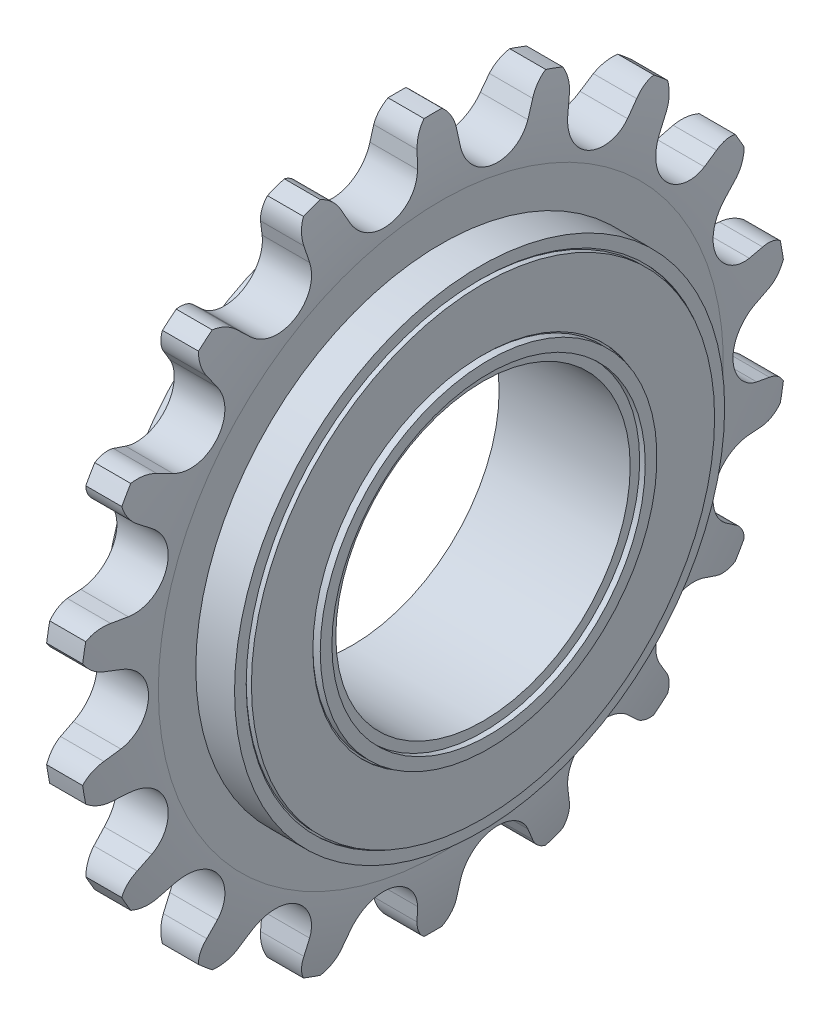
SolidWorks part; units mm, degrees
ref_plane "Front Plane" through (0, 0, 0) normal (0, 0, 1) x (1, 0, 0)
ref_plane "Top Plane" through (0, 0, 0) normal (0, 1, 0) x (1, 0, 0)
ref_plane "Right Plane" through (0, 0, 0) normal (1, 0, 0) x (0, 0, -1)
sketch "Layout with Teeth" plane through (0, 0, 0) normal (1, 0, 0) x (0, 0, -1)
  line L0 (0, 0) -> (0, 66.6612) construction
  line L5 (-11.5756, 65.6485) -> (0, 66.6612) construction
  line L6 (0, 0) -> (-11.5756, 65.6485) construction
  line L7 (0, 0) -> (11.5756, 65.6485) construction
  line L8 (2.3757, 35.5598) -> (-2.3757, 35.5598)
  line L9 (-2.3757, 35.5598) -> (-2.1798, 37.2772)
  line L10 (2.3757, 35.5598) -> (2.1803, 37.2772)
  line L11 (0, 66.6612) -> (11.5756, 65.6485) construction
  circle A0 centre (0, 0) radius 17.4625
  circle A1 centre (0, 0) radius 36.5682
  circle A2 centre (0, 0) radius 39.4882
  circle A7 centre (0, 0) radius 32.5682 construction
  circle A8 centre (0, 0) radius 18.52
  circle A9 centre (0, 0) radius 19.82
  circle A10 centre (0, 0) radius 20.02
  circle A11 centre (0, 0) radius 25.815
  circle A12 centre (0, 0) radius 26.015
  circle A13 centre (0, 0) radius 27.315
  arc A14 (-0.9993, 39.4755) -> (-2.1798, 37.2772) centre (1.1685, 36.8953) ccw
  arc A15 (1.0007, 39.4755) -> (2.1803, 37.2772) centre (-1.1681, 36.8962) cw
  circle A16 centre (6.35, 36.0126) radius 4
  circle A17 centre (-6.35, 36.0126) radius 4
  dimension "D2" = 8
  dimension "D3" = 3.37
  dimension "D4" = 2.92
  dimension "D5" = 78.9764
  dimension "D6" = 73.1364
  dimension "D7" = 34.925
  dimension "D9" = 12.7
  dimension "D11" = 37.04
  dimension "D12" = 39.64
  dimension "D13" = 40.04
  dimension "D14" = 51.63
  dimension "D15" = 52.03
  dimension "D16" = 54.63
  dimension "D18" = 3.37
  dimension "D20" = 8
  dimension "D8" = 13
  dimension "D10" = 20
  dimension "D17" = 1.7285
  dimension "D19" = 1.7285
  dimension "D21" = 2
  dimension "D22" = 4.7514
  dimension "D23" = 11.5756
sketch "Side Layout" plane through (0, 0, 0) normal (0, 0, 1) x (1, 0, 0)
  line L0 (2.8829, 31.4882) -> (2.8829, 27.3125)
  line L1 (2.8829, 27.3125) -> (7.2, 27.3125)
  line L2 (0, -39.4882) -> (0, 39.4882) construction
  line L3 (0, 0) -> (0, 66.6612) construction
  line L4 (2.0077, 39.4882) -> (-2.0077, 39.4882)
  line L5 (-2.8829, 31.4882) -> (-2.8829, 27.3125)
  line L6 (-2.8829, 27.3125) -> (-7.2, 27.3125)
  line L7 (-7.2, 27.3125) -> (-7.2, 25.8125)
  line L8 (-7.58, 25.8125) -> (-4, 25.8125)
  line L9 (-4, 25.8125) -> (-4, 18.9625)
  line L10 (-7.58, 16.4042) -> (7.2, 16.4042)
  line L11 (0, 0) -> (0, 47.8969) construction
  line L12 (7.2, 27.3125) -> (7.2, 25.8125)
  line L13 (7.58, 25.8125) -> (4, 25.8125)
  line L14 (-2.8829, 31.4882) -> (0, 31.4882) construction
  line L18 (-4, 18.9625) -> (-8.2, 18.9625)
  line L19 (-7.58, 17.4625) -> (-8.2, 17.4625)
  line L20 (-8.2, 18.9625) -> (-8.2, 17.4625)
  line L21 (-7.58, 18.9625) -> (-7.58, 25.8125)
  line L22 (4, 18.9625) -> (7.58, 18.9625)
  line L23 (7.2, 18.9625) -> (7.2, 16.4042)
  line L24 (7.58, 18.9625) -> (7.58, 25.8125)
  line L25 (4, 25.8125) -> (4, 18.9625)
  line L26 (-7.58, 17.4625) -> (-7.58, 16.4042)
  arc A0 (-2.0077, 39.4882) -> (-2.8829, 31.4882) centre (34.1171, 31.4882) ccw
  arc A1 (2.0077, 39.4882) -> (2.8829, 31.4882) centre (-34.1171, 31.4882) cw
  point P0 (0, 39.4882)
  point P30 (0, 39.4882)
  point P38 (0, 17.4625)
  dimension "D14" = 37
  dimension "D1" = 9.4083
  dimension "D2" = 4.1757
  dimension "D4" = 1.5
  dimension "D7" = 10.9083
  dimension "D9" = 8
  dimension "D5" = 4.0154
  dimension "D6" = 5.7658
  dimension "D3" = 14.4
  dimension "D10" = 1
  dimension "D11" = 15.16
  dimension "D12" = 1.5
  dimension "D8" = 1.0583
  dimension "D13" = 8
sketch "Threaded Hole Layout" plane through (0, 0, 0) normal (0, 0, 1) x (1, 0, 0)
  line L1 (-7.58, 17.3625) -> (-7.63, 17.2759) construction
  line L2 (-8.191, 16.3042) -> (-8.141, 16.3042) construction
  line L3 (-6.969, 16.3042) -> (-7.019, 16.3908) construction
  line L4 (-7.58, 17.4625) -> (-7.58, 16.4042) construction
  line L5 (-7.58, 16.4042) -> (7.2, 16.4042) construction
  line L6 (-7.63, 17.2759) -> (-7.53, 17.2759)
  line L7 (-7.019, 16.3908) -> (-7.019, 16.3042)
  line L8 (-8.141, 16.3908) -> (-8.141, 16.3042)
  line L9 (-7.63, 17.2759) -> (-8.141, 16.3908)
  line L10 (-7.53, 17.2759) -> (-7.58, 17.3625) construction
  line L13 (-8.141, 16.3908) -> (-8.191, 16.3042) construction
  line L14 (-8.141, 16.3042) -> (-7.019, 16.3042)
  line L15 (-7.019, 16.3042) -> (-6.969, 16.3042) construction
  line L16 (-7.019, 16.3908) -> (-7.53, 17.2759)
  circle A0 centre (-7.58, 16.6569) radius 0.3528 construction
  dimension "D1" = 1.0583
  dimension "D2" = 0.1
  dimension "D3" = 0.1
  dimension "D4" = 0.05
sketch "Sketch8" plane through (0, 0, 0) normal (1, 0, 0) x (0, 0, -1)
  line L0 (0, 0) -> (-11.5756, 65.6485) construction
  circle A0 centre (0, 0) radius 36.5682 construction
  point P0 (-6.35, 36.0126)
  point P1 (-28.0129, 23.5056)
  point P2 (-18.2841, 31.669)
  point P4 (6.35, 36.0126)
  point P5 (18.2841, 31.669)
  point P6 (28.0129, 23.5056)
  point P7 (34.3629, 12.5071)
  point P8 (36.5682, 0)
  point P9 (34.3629, -12.5071)
  point P10 (28.0129, -23.5056)
  point P11 (18.2841, -31.669)
  point P12 (6.35, -36.0126)
  point P13 (-6.35, -36.0126)
  point P14 (-18.2841, -31.669)
  point P15 (-28.0129, -23.5056)
  point P16 (-34.3629, -12.5071)
  point P17 (-36.5682, 0)
  point P18 (-34.3629, 12.5071)
  point P19 (0, 0)
  dimension "D1" = 18
ref_axis "Axis1" through (0, 0, 0) along (1, 0, 0)
sketch "Sketch4" plane through (0, 0, 0) normal (1, 0, 0) x (0, 0, -1)
  line L0 (-2.3757, 35.5598) -> (-2.1798, 37.2772) construction
  line L1 (2.3757, 35.5598) -> (2.1803, 37.2772) construction
  line L2 (0, 0) -> (-11.5756, 65.6485) construction
  line L3 (0, 0) -> (11.5756, 65.6485) construction
  line L8 (-2.3758, 35.5593) -> (-2.1798, 37.2772)
  line L9 (2.3757, 35.5603) -> (2.1803, 37.2772)
  line L10 (0, 0) -> (-5.6554, 32.0734)
  line L11 (0, 0) -> (5.6554, 32.0734)
  arc A1 (-0.9993, 39.4755) -> (-2.1798, 37.2772) centre (1.1685, 36.8953) ccw construction
  arc A2 (2.1803, 37.2772) -> (1.0007, 39.4755) centre (-1.1681, 36.8962) ccw construction
  circle A3 centre (-6.35, 36.0126) radius 4 construction
  circle A4 centre (6.35, 36.0126) radius 4 construction
  arc A7 (-0.9993, 39.4755) -> (-2.1798, 37.2772) centre (1.1685, 36.8953) ccw
  arc A9 (2.1803, 37.2772) -> (1.0007, 39.4755) centre (-1.1681, 36.8962) ccw
  arc A10 (-5.6554, 32.0734) -> (-2.3758, 35.5593) centre (-6.35, 36.0126) ccw
  arc A11 (2.3757, 35.5603) -> (5.6554, 32.0734) centre (6.35, 36.0126) ccw
  arc A14 (1.0007, 39.4755) -> (-0.9993, 39.4755) centre (0, 0) ccw
extrude "Boss-Extrude1" add sketch "Sketch4" along normal mid plane 17
pattern_circular "CirPattern2" count 18 over 360 about axis through (0, 0, 0) along (1, 0, 0) of "Boss-Extrude1"
sketch "Sketch6" plane through (0, 0, 0) normal (0, 0, 1) x (1, 0, 0)
  line L0 (7.2, 27.3125) -> (7.2, 25.8125) construction
  line L1 (0, 39.4882) -> (0, 16.4042) construction
  line L2 (7.58, 18.9625) -> (7.58, 25.8125) construction
  line L3 (2.0077, 39.4882) -> (-2.0077, 39.4882) construction
  line L4 (-10, 39.4882) -> (-10, 0)
  line L5 (-2.0077, 39.4882) -> (-10, 39.4882)
  line L6 (10, 39.4882) -> (10, 0)
  line L7 (2.0077, 39.4882) -> (10, 39.4882)
  line L8 (7, 26.0125) -> (7.2, 26.0125)
  line L9 (-7, 26.0125) -> (-7, 25.8125)
  line L10 (-7.2, 26.0125) -> (-7, 26.0125)
  line L11 (7, 25.8125) -> (7, 26.0125)
  line L12 (7.38, 18.7625) -> (8.2, 18.7625)
  line L13 (7.38, 18.9625) -> (7.38, 18.7625)
  line L14 (2.8829, 31.4882) -> (2.8829, 27.3125)
  line L15 (2.8829, 27.3125) -> (7.2, 27.3125)
  line L16 (7.2, 27.3125) -> (7.2, 26.0125)
  line L17 (7.58, 25.8125) -> (7, 25.8125)
  line L18 (7.58, 18.9625) -> (7.58, 25.8125)
  line L19 (7.38, 18.9625) -> (7.58, 18.9625)
  line L20 (8.2, 18.7625) -> (8.2, 17.4625)
  line L21 (7.58, 17.4625) -> (8.2, 17.4625)
  line L22 (-7.58, 17.4625) -> (-8.2, 17.4625) construction
  line L23 (-7.2, 27.3125) -> (-7.2, 25.8125) construction
  line L24 (-7.58, 18.9625) -> (-7.58, 25.8125) construction
  line L25 (-7.58, 16.4042) -> (7.2, 16.4042) construction
  line L26 (-2.8829, 27.3125) -> (-7.2, 27.3125) construction
  line L27 (-7.58, 25.8125) -> (-4, 25.8125) construction
  line L28 (7.58, 25.8125) -> (4, 25.8125) construction
  line L29 (2.0077, 39.4882) -> (-2.0077, 39.4882) construction
  line L35 (7.58, 17.4625) -> (7.58, 16.4042)
  line L65 (7.58, 16.4042) -> (-7.2, 16.4042)
  line L68 (-7.2, 18.9625) -> (-7.2, 16.4042)
  line L69 (-7.2, 18.9625) -> (-7.58, 18.9625)
  line L70 (-7.58, 18.9625) -> (-7.58, 25.8125)
  line L71 (-7.58, 25.8125) -> (-7, 25.8125)
  line L72 (-7.2, 27.3125) -> (-7.2, 26.0125)
  line L73 (-2.8829, 27.3125) -> (-7.2, 27.3125)
  line L74 (-2.8829, 31.4882) -> (-2.8829, 27.3125)
  line L75 (10, 0) -> (-10, 0)
  arc A0 (2.0077, 39.4882) -> (2.8829, 31.4882) centre (-34.1171, 31.4882) cw
  arc A1 (-2.8829, 31.4882) -> (-2.0077, 39.4882) centre (34.1171, 31.4882) cw
  arc A2 (2.8829, 31.4882) -> (2.0077, 39.4882) centre (-34.1171, 31.4882) ccw construction
  arc A3 (-2.0077, 39.4882) -> (-2.8829, 31.4882) centre (34.1171, 31.4882) ccw construction
  dimension "D1" = 0.2
  dimension "D2" = 20
  dimension "D3" = 0.82
  dimension "D4" = 0.2
  dimension "D5" = 0.2
  dimension "D6" = 1.3
  dimension "D7" = 0.38
  dimension "D8" = 2.5583
revolve "Cut-Revolve1" cut sketch "Sketch6" angle 360 about axis through (0, 0, 0) along (1, 0, 0)
sketch "Sketch7" plane through (0, 0, 0) normal (0, 0, 1) x (1, 0, 0)
  line L0 (-7.63, 17.2759) -> (-8.141, 16.3908) construction
  line L1 (-7.63, 17.2759) -> (-7.53, 17.2759) construction
  line L2 (-7.019, 16.3908) -> (-7.53, 17.2759) construction
  line L3 (-8.141, 16.3042) -> (-7.019, 16.3042) construction
  line L4 (-8.141, 16.3908) -> (-8.141, 16.3042) construction
  line L5 (-7.019, 16.3908) -> (-7.019, 16.3042) construction
  line L6 (-7.63, 17.2759) -> (-8.141, 16.3908)
  line L7 (-7.63, 17.2759) -> (-7.53, 17.2759)
  line L8 (-7.019, 16.3908) -> (-7.53, 17.2759)
  line L9 (-8.141, 16.3042) -> (-7.019, 16.3042)
  line L10 (-8.141, 16.3908) -> (-8.141, 16.3042)
  line L11 (-7.019, 16.3908) -> (-7.019, 16.3042)
revolve "Cut-Revolve2" cut sketch "Sketch7" angle 360 about axis through (0, 0, 0) along (1, 0, 0)
equation "\"D8@Side Layout\"=25.4/24"
